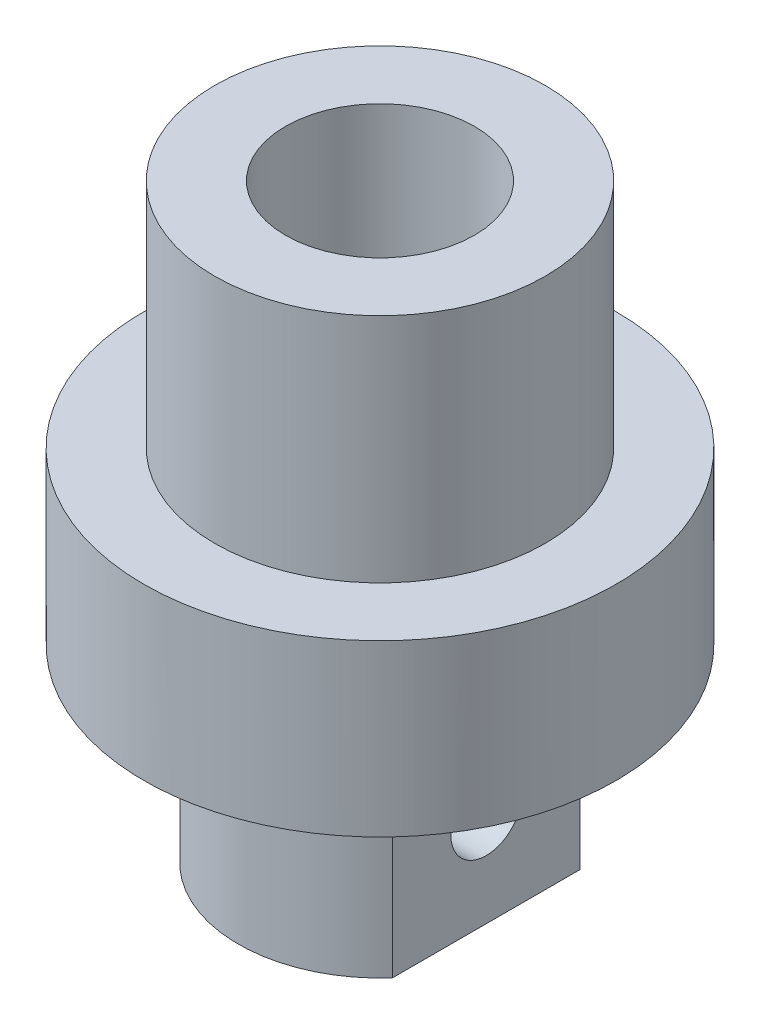
SolidWorks part; units mm, degrees
ref_plane "Front Plane" through (0, 0, 0) normal (0, 0, 1) x (1, 0, 0)
ref_plane "Top Plane" through (0, 0, 0) normal (0, 1, 0) x (1, 0, 0)
ref_plane "Right Plane" through (0, 0, 0) normal (1, 0, 0) x (0, 0, -1)
sketch "Sketch1" plane through (0, 0, 0) normal (0, 1, 0) x (1, 0, 0)
  circle A0 centre (0, 0) radius 10
extrude "Boss-Extrude2" add sketch "Sketch1" along normal blind 25
sketch "Sketch2" plane through (0, 25, 0) normal (0, 1, 0) x (1, 0, 0)
  circle A0 centre (0, 0) radius 10
  circle A1 centre (0, 0) radius 7
extrude "Cut-Extrude1" cut sketch "Sketch2" against normal blind 9.8
sketch "Sketch3" plane through (0, 0, 0) normal (0, -1, 0) x (1, 0, 0)
  circle A0 centre (0, 0) radius 10
  circle A1 centre (0, 0) radius 6
extrude "Cut-Extrude2" cut sketch "Sketch3" against normal blind 8
sketch "Sketch4" plane through (0, 25, 0) normal (0, 1, 0) x (1, 0, 0)
  circle A0 centre (0, 0) radius 4
extrude "Cut-Extrude3" cut sketch "Sketch4" against normal blind 15
sketch "Sketch5" plane through (0, 0, 0) normal (0, -1, 0) x (1, 0, 0)
  circle A0 centre (0, 0) radius 2.75
extrude "Cut-Extrude4" cut sketch "Sketch5" against normal blind 11
sketch "Sketch6" plane through (0, 0, 0) normal (0, -1, 0) x (1, 0, 0)
  line L1 (4.5, 0) -> (4.5, 3.9686)
  line L2 (4.5, 0) -> (4.5, -3.9686)
  arc A1 (4.5, -3.9686) -> (4.5, 3.9686) centre (0, 0) ccw
extrude "Cut-Extrude5" cut sketch "Sketch6" against normal up to surface (8 mm away) up to face at (0, 8, -6)
sketch "Sketch7" plane through (4.5, 0, 0) normal (1, 0, 0) x (0, 0, -1)
  circle A0 centre (0, 4) radius 1.5
extrude "Cut-Extrude6" cut sketch "Sketch7" against normal blind 4
